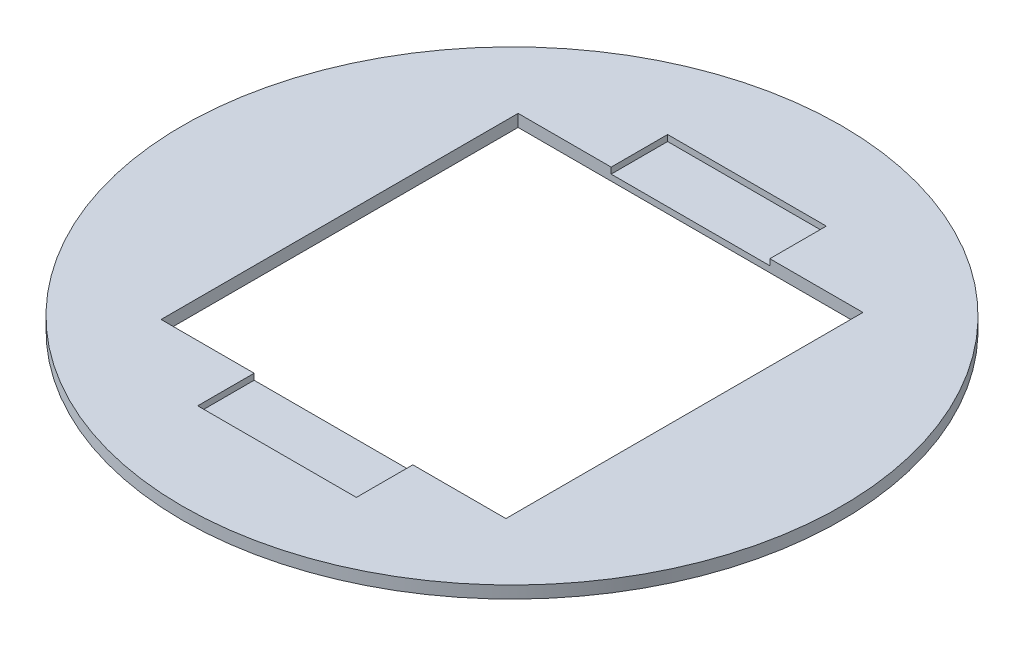
SolidWorks part; units mm, degrees
ref_plane "Front Plane" through (0, 0, 0) normal (0, 0, 1) x (1, 0, 0)
ref_plane "Top Plane" through (0, 0, 0) normal (0, 1, 0) x (1, 0, 0)
ref_plane "Right Plane" through (0, 0, 0) normal (1, 0, 0) x (0, 0, -1)
sketch "Sketch1" plane through (0, 0, 0) normal (0, 1, 0) x (1, 0, 0)
  circle A0 centre (0, 0) radius 54
  dimension "D1" = 108
extrude "Boss-Extrude1" add sketch "Sketch1" along normal blind 2
sketch "Sketch2" plane through (0, 2, 0) normal (0, 1, 0) x (1, 0, 0)
  line L1 (28.25, -29.25) -> (-28.25, -29.25)
  line L2 (28.25, -29.25) -> (28.25, 29.25)
  line L3 (28.25, 29.25) -> (-28.25, 29.25)
  line L4 (-28.25, -29.25) -> (-28.25, 29.25)
  line L5 (28.25, -29.25) -> (-28.25, 29.25) construction
  line L6 (28.25, 29.25) -> (-28.25, -29.25) construction
  point P0 (0, 0)
  dimension "D1" = 56.5
  dimension "D2" = 58.5
extrude "Cut-Extrude1" cut sketch "Sketch2" against normal up to surface (2 mm away) up to face at (0, 0, 54)
sketch "Sketch3" plane through (0, 2, 0) normal (0, 1, 0) x (1, 0, 0)
  line L0 (28.25, 29.25) -> (-28.25, 29.25) construction
  line L1 (-13, 38.5) -> (13, 38.5)
  line L2 (-13, 38.5) -> (-13, 29.25)
  line L3 (-13, 29.25) -> (13, 29.25)
  line L4 (13, 38.5) -> (13, 29.25)
  line L5 (-13, 38.5) -> (13, 29.25) construction
  line L6 (-13, 29.25) -> (13, 38.5) construction
  line L7 (0, 33.875) -> (0, 0) construction
  line L8 (-28.25, 0) -> (28.25, 0) construction
  line L9 (-28.25, 29.25) -> (-28.25, -29.25) construction
  line L10 (28.25, -29.25) -> (28.25, 29.25) construction
  line L11 (13, -38.5) -> (13, -29.25)
  line L12 (-13, -29.25) -> (13, -29.25)
  line L13 (-13, -29.25) -> (13, -38.5) construction
  line L14 (-13, -38.5) -> (-13, -29.25)
  line L15 (-13, -38.5) -> (13, -29.25) construction
  line L16 (-13, -38.5) -> (13, -38.5)
  point P0 (0, 33.875)
  dimension "D1" = 26
  dimension "D2" = 9.25
extrude "Cut-Extrude2" cut sketch "Sketch3" against normal blind 1
